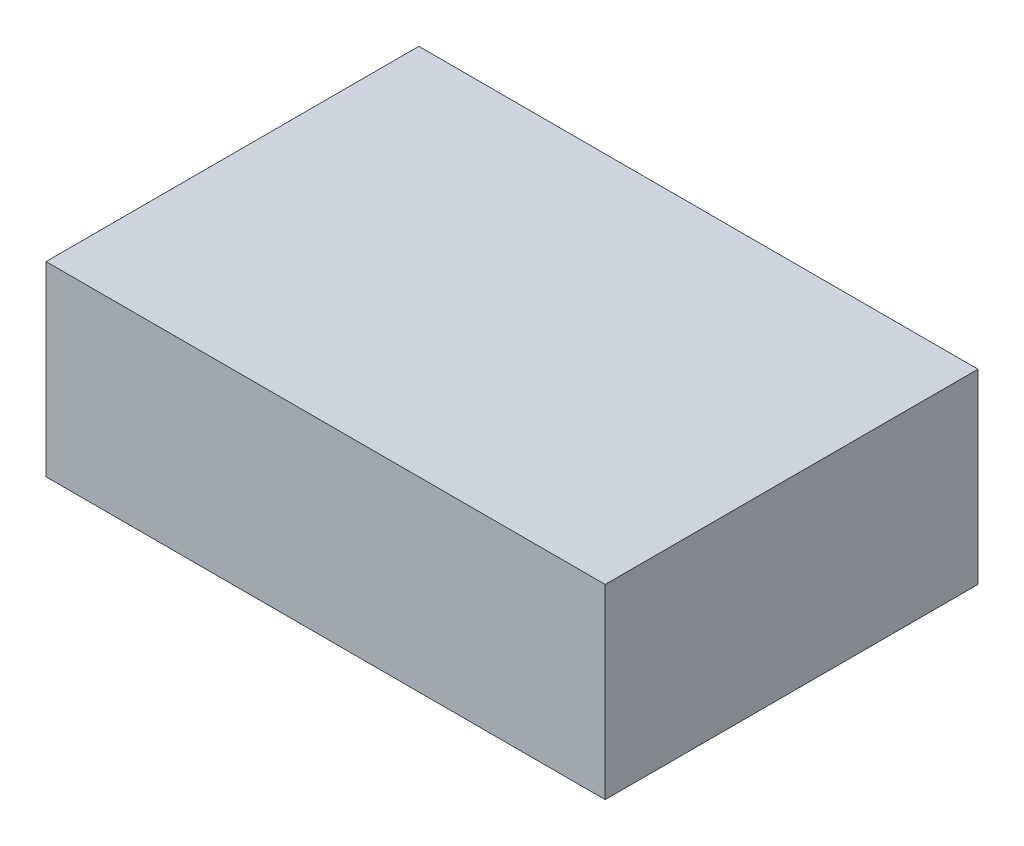
SolidWorks part; units mm, degrees
ref_plane "Plan de face" through (0, 0, 0) normal (0, 0, 1) x (1, 0, 0)
ref_plane "Plan de dessus" through (0, 0, 0) normal (0, 1, 0) x (1, 0, 0)
ref_plane "Plan de droite" through (0, 0, 0) normal (1, 0, 0) x (0, 0, -1)
sketch "Esquisse1" plane through (0, 0, 0) normal (0, 1, 0) x (1, 0, 0)
  line L1 (-45, -30) -> (45, -30)
  line L2 (-45, -30) -> (-45, 30)
  line L3 (-45, 30) -> (45, 30)
  line L4 (45, -30) -> (45, 30)
  line L5 (-45, -30) -> (45, 30) construction
  line L6 (-45, 30) -> (45, -30) construction
  point P0 (0, 0)
  dimension "D1" = 90
  dimension "D2" = 60
extrude "Boss.-Extru.1" add sketch "Esquisse1" along normal blind 30
